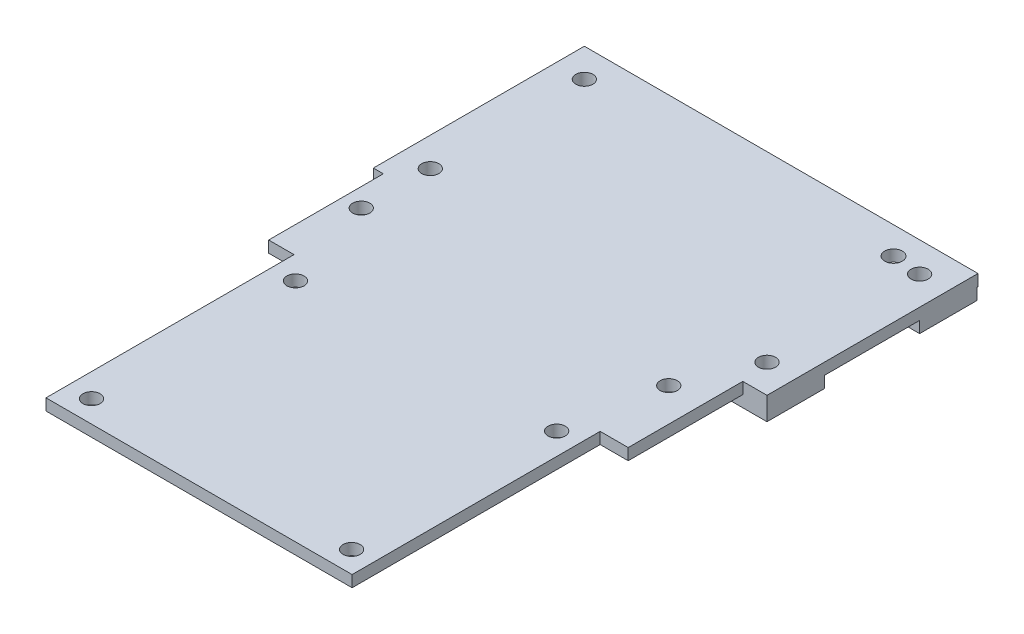
SolidWorks part; units mm, degrees
ref_plane "Front Plane" through (0, 0, 0) normal (0, 0, 1) x (1, 0, 0)
ref_plane "Top Plane" through (0, 0, 0) normal (0, 1, 0) x (1, 0, 0)
ref_plane "Right Plane" through (0, 0, 0) normal (1, 0, 0) x (0, 0, -1)
sketch "Sketch1" plane through (0, 0, 0) normal (0, 1, 0) x (1, 0, 0)
  line L0 (-73.4171, 38.1679) -> (-63.4171, 38.1679)
  line L1 (-73.4171, 38.1679) -> (-73.4171, 28.1679)
  line L2 (-73.4171, 28.1679) -> (-63.4171, 28.1679)
  line L3 (-63.4171, 38.1679) -> (-63.4171, 28.1679)
  line L4 (-73.3569, 11.2123) -> (-63.3569, 11.2123)
  line L5 (-73.3569, 11.2123) -> (-73.3569, 1.2123)
  line L6 (-73.3569, 1.2123) -> (-63.3569, 1.2123)
  line L7 (-63.3569, 11.2123) -> (-63.3569, 1.2123)
  line L8 (-14.6983, 11.33) -> (-4.6983, 11.33)
  line L9 (-14.6983, 11.33) -> (-14.6983, 1.33)
  line L10 (-14.6983, 1.33) -> (-4.6983, 1.33)
  line L11 (-4.6983, 11.33) -> (-4.6983, 1.33)
  line L12 (-14.6983, 37.9743) -> (-4.6983, 37.9743)
  line L13 (-14.6983, 37.9743) -> (-14.6983, 27.9743)
  line L14 (-14.6983, 27.9743) -> (-4.6983, 27.9743)
  line L15 (-4.6983, 37.9743) -> (-4.6983, 27.9743)
  circle A0 centre (-68.4171, 33.1679) radius 1.5
  circle A1 centre (-9.6983, 32.9743) radius 1.5
  circle A2 centre (-68.3569, 6.2123) radius 1.5
  circle A3 centre (-9.6983, 6.33) radius 1.5
extrude "Boss-Extrude1" add sketch "Sketch1" along normal blind 2
sketch "Sketch2" plane through (0, 2, 0) normal (0, 1, 0) x (1, 0, 0)
  line L0 (-14.6983, 1.33) -> (-4.6983, 1.33) construction
  line L1 (-73.4171, 38.1679) -> (-4.6983, 38.1679)
  line L2 (-73.4171, 38.1679) -> (-73.4171, 1.33)
  line L3 (-73.4171, 1.33) -> (-4.6983, 1.33)
  line L4 (-4.6983, 38.1679) -> (-4.6983, 1.33)
  circle A0 centre (-68.4171, 33.1679) radius 1.5
  circle A1 centre (-9.6983, 32.9743) radius 1.5
  circle A2 centre (-9.6983, 6.33) radius 1.5
  circle A3 centre (-68.3569, 6.2123) radius 1.5
extrude "Boss-Extrude2" add sketch "Sketch2" along normal blind 2
sketch "Sketch3" plane through (0, 4, 0) normal (0, 1, 0) x (1, 0, 0)
  line L5 (-71.6771, 36.3179) -> (-8.9171, 36.3179)
  line L6 (-71.6771, 36.3179) -> (-71.6771, -8.6821)
  line L7 (-71.6771, -8.6821) -> (-8.9171, -8.6821)
  line L8 (-8.9171, 36.3179) -> (-8.9171, -8.6821)
  circle A0 centre (-68.4171, 33.1679) radius 1.5
  circle A1 centre (-68.3569, 6.2123) radius 1.5
  dimension "D1" = 62.76
  dimension "D2" = 45
  dimension "D3" = 3.15
  dimension "D4" = 3.26
extrude "Boss-Extrude3" add sketch "Sketch3" against normal blind 2
sketch "Sketch4" plane through (0, 4, 0) normal (0, 1, 0) x (1, 0, 0)
  circle A0 centre (-9.6983, 6.33) radius 1.5
  circle A1 centre (-9.6983, 32.9743) radius 1.5
extrude "Cut-Extrude1" cut sketch "Sketch4" against normal blind 2
sketch "Sketch5" plane through (0, 4, 0) normal (0, 1, 0) x (1, 0, 0)
  line L0 (-71.6771, 36.3179) -> (-71.6771, -8.6821) construction
  line L1 (-71.6771, -8.6821) -> (-8.9171, -8.6821) construction
  line L2 (-8.9171, 36.3179) -> (-8.9171, -8.6821) construction
  line L3 (-71.6771, 36.3179) -> (-8.9171, 36.3179) construction
  circle A0 centre (-68.4171, -5.7821) radius 1.5
  circle A1 centre (-14.7371, -5.7821) radius 1.5
  circle A2 centre (-14.7371, 33.4179) radius 1.5
  dimension "D1" = 3
  dimension "D3" = 2.9
  dimension "D4" = 3
  dimension "D5" = 3
  dimension "D7" = 2.9
  dimension "D8" = 5.82
  dimension "D9" = 2.9
  dimension "D2" = 3.26
  dimension "D6" = 5.82
extrude "Cut-Extrude2" cut sketch "Sketch5" against normal blind 2
sketch "Sketch6" plane through (0, 4, 0) normal (0, 1, 0) x (1, 0, 0)
  line L0 (-14.6983, 34.9174) -> (-14.6983, 31.9184) construction
  circle A0 centre (-14.6983, 33.4179) radius 1.5387
extrude "Cut-Extrude3" cut sketch "Sketch6" against normal blind 4
sketch "Sketch7" plane through (0, 4, 0) normal (0, 1, 0) x (1, 0, 0)
  line L1 (-67.2517, -18.6821) -> (-13.8117, -18.6821)
  line L2 (-67.2517, -18.6821) -> (-67.2517, -61.9821)
  line L3 (-67.2517, -61.9821) -> (-13.8117, -61.9821)
  line L4 (-13.8117, -18.6821) -> (-13.8117, -61.9821)
  line L5 (-71.6771, -8.6821) -> (-8.9171, -8.6821)
  line L6 (-71.6771, -8.6821) -> (-71.6771, -18.6821)
  line L7 (-71.6771, -18.6821) -> (-8.9171, -18.6821)
  line L8 (-8.9171, -8.6821) -> (-8.9171, -18.6821)
  circle A0 centre (-17.6517, -22.4321) radius 1.5
  circle A1 centre (-17.6517, -58.2321) radius 1.5
  circle A2 centre (-63.1517, -58.1321) radius 1.5
  circle A3 centre (-63.1517, -22.5321) radius 1.5
  line M17 (-71.6771, -8.6821) -> (-8.9171, -8.6821)
  dimension "D4" = 3
  dimension "D5" = 3.84
  dimension "D7" = 3.84
  dimension "D8" = 3.75
  dimension "D9" = 3.85
  dimension "D10" = 4.1
  dimension "D11" = 4.1
  dimension "D12" = 3.85
  dimension "D1" = 43.3
  dimension "D2" = 53.44
  dimension "D3" = 10
  dimension "D6" = 3.75
extrude "Boss-Extrude4" add sketch "Sketch7" against normal blind 2 contours L4 L1 L2 L3 A3 A2 A1 A0 | L8 L6 L7 L1 M17
